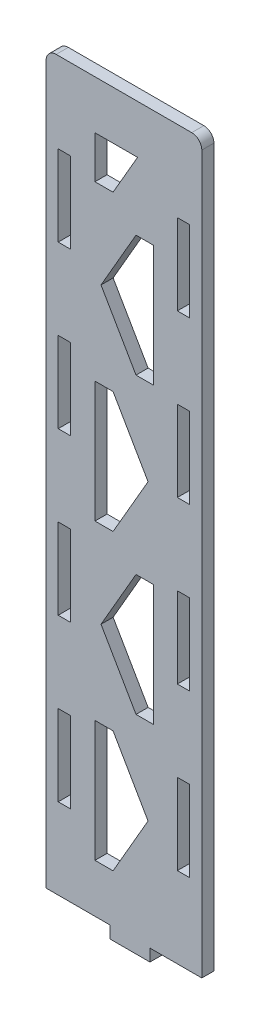
SolidWorks part; units mm, degrees
ref_plane "Front Plane" through (0, 0, 0) normal (0, 0, 1) x (1, 0, 0)
ref_plane "Top Plane" through (0, 0, 0) normal (0, 1, 0) x (1, 0, 0)
ref_plane "Right Plane" through (0, 0, 0) normal (1, 0, 0) x (0, 0, -1)
sketch "Sketch1" plane through (0, 0, 0) normal (0, 0, 1) x (1, 0, 0)
  line L0 (-16.275, -90) -> (-16.275, 90) construction
  line L1 (-19.275, -90) -> (19.275, -90)
  line L2 (-19.275, -90) -> (-19.275, 90)
  line L3 (-19.275, 90) -> (19.275, 90)
  line L4 (19.275, -90) -> (19.275, 90)
  line L5 (-19.275, -90) -> (19.275, 90) construction
  line L6 (-19.275, 90) -> (19.275, -90) construction
  line L7 (16.275, -90) -> (16.275, 90) construction
  line L8 (6.4417, -93) -> (16.275, -93) construction
  line L33 (-3.3917, -93) -> (6.4417, -93)
  line L34 (-3.3917, -93) -> (-3.3917, -90)
  line L35 (-3.3917, -90) -> (6.4417, -90)
  line L36 (6.4417, -93) -> (6.4417, -90)
  line L37 (-3.3917, -93) -> (6.4417, -90) construction
  line L38 (-3.3917, -90) -> (6.4417, -93) construction
  line L43 (-3.3917, -93) -> (-13.225, -93) construction
  line L44 (13.225, 90) -> (13.225, 70) construction
  line L45 (13.225, -10) -> (16.275, -10)
  line L46 (13.225, -10) -> (13.225, -30)
  line L47 (13.225, -30) -> (16.275, -30)
  line L48 (16.275, -10) -> (16.275, -30)
  line L49 (13.225, -10) -> (16.275, -30) construction
  line L50 (13.225, -30) -> (16.275, -10) construction
  line L51 (13.225, 10) -> (16.275, 10)
  line L52 (13.225, 10) -> (13.225, 30)
  line L53 (13.225, 30) -> (16.275, 30)
  line L54 (16.275, 10) -> (16.275, 30)
  line L55 (13.225, 10) -> (16.275, 30) construction
  line L56 (13.225, 30) -> (16.275, 10) construction
  line L57 (13.225, 50) -> (16.275, 50)
  line L58 (13.225, 50) -> (13.225, 70)
  line L59 (13.225, 70) -> (16.275, 70)
  line L60 (16.275, 50) -> (16.275, 70)
  line L61 (13.225, 50) -> (16.275, 70) construction
  line L62 (13.225, 70) -> (16.275, 50) construction
  line L63 (13.225, -50) -> (16.275, -50)
  line L64 (13.225, -50) -> (13.225, -70)
  line L65 (13.225, -70) -> (16.275, -70)
  line L66 (16.275, -50) -> (16.275, -70)
  line L67 (13.225, -50) -> (16.275, -70) construction
  line L68 (13.225, -70) -> (16.275, -50) construction
  line L69 (13.225, 50) -> (13.225, 30) construction
  line L70 (13.225, 10) -> (13.225, -10) construction
  line L71 (13.225, -30) -> (13.225, -50) construction
  line L72 (13.225, -70) -> (13.225, -90) construction
  line L73 (0, -781.5075) -> (0, 49218.4925) construction
  line L74 (-13.225, 70) -> (-16.275, 70)
  line L75 (-16.275, 50) -> (-16.275, 70)
  line L76 (-13.225, 50) -> (-16.275, 50)
  line L77 (-13.225, 50) -> (-13.225, 70)
  line L78 (-13.225, 30) -> (-16.275, 30)
  line L79 (-16.275, 10) -> (-16.275, 30)
  line L80 (-13.225, 10) -> (-16.275, 10)
  line L81 (-13.225, 10) -> (-13.225, 30)
  line L82 (-13.225, -30) -> (-16.275, -30)
  line L83 (-16.275, -10) -> (-16.275, -30)
  line L84 (-13.225, -10) -> (-16.275, -10)
  line L85 (-13.225, -10) -> (-13.225, -30)
  line L86 (-13.225, -70) -> (-16.275, -70)
  line L87 (-16.275, -50) -> (-16.275, -70)
  line L88 (-13.225, -50) -> (-16.275, -50)
  line L89 (-13.225, -50) -> (-13.225, -70)
  point P0 (0, 0)
  point P30 (1.525, -91.5)
  point P35 (14.75, 20)
  point P39 (14.75, -20)
  point P47 (14.75, 60)
  point P52 (14.75, -60)
  dimension "D1" = 26.45
  dimension "D2" = 180
  dimension "D5" = 3
  dimension "D6" = 3.05
  dimension "D3" = 3
  dimension "D4" = 3
extrude "Boss-Extrude1" add sketch "Sketch1" along normal blind 3
sketch "Sketch2" plane through (-113.675, -93, 3) normal (0, 0, -1) x (-1, 0, 0)
  line L1 (-234.6603, 8.6269) -> (-251.9808, 8.6269)
  line L2 (-251.9808, 8.6269) -> (-260.641, -6.3731)
  line L3 (-260.641, -6.3731) -> (-251.9808, -21.3731)
  line L4 (-251.9808, -21.3731) -> (-234.6603, -21.3731)
  line L5 (-234.6603, -21.3731) -> (-226, -6.3731)
  line L6 (-226, -6.3731) -> (-234.6603, 8.6269)
  line L7 (-192.6603, 8.6269) -> (-209.9808, 8.6269)
  line L8 (-209.9808, 8.6269) -> (-218.641, -6.3731)
  line L9 (-218.641, -6.3731) -> (-209.9808, -21.3731)
  line L10 (-209.9808, -21.3731) -> (-192.6603, -21.3731)
  line L11 (-192.6603, -21.3731) -> (-184, -6.3731)
  line L12 (-184, -6.3731) -> (-192.6603, 8.6269)
  line L13 (-150.6603, 8.6269) -> (-167.9808, 8.6269)
  line L14 (-167.9808, 8.6269) -> (-176.641, -6.3731)
  line L15 (-176.641, -6.3731) -> (-167.9808, -21.3731)
  line L16 (-167.9808, -21.3731) -> (-150.6603, -21.3731)
  line L17 (-150.6603, -21.3731) -> (-142, -6.3731)
  line L18 (-142, -6.3731) -> (-150.6603, 8.6269)
  line L19 (-108.6603, 8.6269) -> (-125.9808, 8.6269)
  line L20 (-125.9808, 8.6269) -> (-134.641, -6.3731)
  line L21 (-134.641, -6.3731) -> (-125.9808, -21.3731)
  line L22 (-125.9808, -21.3731) -> (-108.6603, -21.3731)
  line L23 (-108.6603, -21.3731) -> (-100, -6.3731)
  line L24 (-100, -6.3731) -> (-108.6603, 8.6269)
  line L25 (-66.6603, 8.6269) -> (-83.9808, 8.6269)
  line L26 (-83.9808, 8.6269) -> (-92.641, -6.3731)
  line L27 (-92.641, -6.3731) -> (-83.9808, -21.3731)
  line L28 (-83.9808, -21.3731) -> (-66.6603, -21.3731)
  line L29 (-66.6603, -21.3731) -> (-58, -6.3731)
  line L30 (-58, -6.3731) -> (-66.6603, 8.6269)
  line L31 (-24.6603, 8.6269) -> (-41.9808, 8.6269)
  line L32 (-41.9808, 8.6269) -> (-50.641, -6.3731)
  line L33 (-50.641, -6.3731) -> (-41.9808, -21.3731)
  line L34 (-41.9808, -21.3731) -> (-24.6603, -21.3731)
  line L35 (-24.6603, -21.3731) -> (-16, -6.3731)
  line L36 (-16, -6.3731) -> (-24.6603, 8.6269)
  line L37 (17.3397, 8.6269) -> (0.0192, 8.6269)
  line L38 (0.0192, 8.6269) -> (-8.641, -6.3731)
  line L39 (-8.641, -6.3731) -> (0.0192, -21.3731)
  line L40 (0.0192, -21.3731) -> (17.3397, -21.3731)
  line L41 (17.3397, -21.3731) -> (26, -6.3731)
  line L42 (26, -6.3731) -> (17.3397, 8.6269)
  line L43 (59.3397, 8.6269) -> (42.0192, 8.6269)
  line L44 (42.0192, 8.6269) -> (33.359, -6.3731)
  line L45 (33.359, -6.3731) -> (42.0192, -21.3731)
  line L46 (42.0192, -21.3731) -> (59.3397, -21.3731)
  line L47 (59.3397, -21.3731) -> (68, -6.3731)
  line L48 (68, -6.3731) -> (59.3397, 8.6269)
  line L49 (-171.6603, 45) -> (-188.9808, 45)
  line L50 (-188.9808, 45) -> (-197.641, 30)
  line L51 (-197.641, 30) -> (-188.9808, 15)
  line L52 (-188.9808, 15) -> (-171.6603, 15)
  line L53 (-171.6603, 15) -> (-163, 30)
  line L54 (-163, 30) -> (-171.6603, 45)
  line L55 (-129.6603, 45) -> (-146.9808, 45)
  line L56 (-146.9808, 45) -> (-155.641, 30)
  line L57 (-155.641, 30) -> (-146.9808, 15)
  line L58 (-146.9808, 15) -> (-129.6603, 15)
  line L59 (-129.6603, 15) -> (-121, 30)
  line L60 (-121, 30) -> (-129.6603, 45)
  line L61 (-87.6603, 45) -> (-104.9808, 45)
  line L62 (-104.9808, 45) -> (-113.641, 30)
  line L63 (-113.641, 30) -> (-104.9808, 15)
  line L64 (-104.9808, 15) -> (-87.6603, 15)
  line L65 (-87.6603, 15) -> (-79, 30)
  line L66 (-79, 30) -> (-87.6603, 45)
  line L67 (-45.6603, 45) -> (-62.9808, 45)
  line L68 (-62.9808, 45) -> (-71.641, 30)
  line L69 (-71.641, 30) -> (-62.9808, 15)
  line L70 (-62.9808, 15) -> (-45.6603, 15)
  line L71 (-45.6603, 15) -> (-37, 30)
  line L72 (-37, 30) -> (-45.6603, 45)
  line L73 (-3.6603, 45) -> (-20.9808, 45)
  line L74 (-20.9808, 45) -> (-29.641, 30)
  line L75 (-29.641, 30) -> (-20.9808, 15)
  line L76 (-20.9808, 15) -> (-3.6603, 15)
  line L77 (-3.6603, 15) -> (5, 30)
  line L78 (5, 30) -> (-3.6603, 45)
  line L79 (38.3397, 45) -> (21.0192, 45)
  line L80 (21.0192, 45) -> (12.359, 30)
  line L81 (12.359, 30) -> (21.0192, 15)
  line L82 (21.0192, 15) -> (38.3397, 15)
  line L83 (38.3397, 15) -> (47, 30)
  line L84 (47, 30) -> (38.3397, 45)
  line L85 (80.3397, 45) -> (63.0192, 45)
  line L86 (63.0192, 45) -> (54.359, 30)
  line L87 (54.359, 30) -> (63.0192, 15)
  line L88 (63.0192, 15) -> (80.3397, 15)
  line L89 (80.3397, 15) -> (89, 30)
  line L90 (89, 30) -> (80.3397, 45)
  line L91 (-150.6603, 81.3731) -> (-167.9808, 81.3731)
  line L92 (-167.9808, 81.3731) -> (-176.641, 66.3731)
  line L93 (-176.641, 66.3731) -> (-167.9808, 51.3731)
  line L94 (-167.9808, 51.3731) -> (-150.6603, 51.3731)
  line L95 (-150.6603, 51.3731) -> (-142, 66.3731)
  line L96 (-142, 66.3731) -> (-150.6603, 81.3731)
  line L97 (-108.6603, 81.3731) -> (-125.9808, 81.3731)
  line L98 (-125.9808, 81.3731) -> (-134.641, 66.3731)
  line L99 (-134.641, 66.3731) -> (-125.9808, 51.3731)
  line L100 (-125.9808, 51.3731) -> (-108.6603, 51.3731)
  line L101 (-108.6603, 51.3731) -> (-100, 66.3731)
  line L102 (-100, 66.3731) -> (-108.6603, 81.3731)
  line L103 (-66.6603, 81.3731) -> (-83.9808, 81.3731)
  line L104 (-83.9808, 81.3731) -> (-92.641, 66.3731)
  line L105 (-92.641, 66.3731) -> (-83.9808, 51.3731)
  line L106 (-83.9808, 51.3731) -> (-66.6603, 51.3731)
  line L107 (-66.6603, 51.3731) -> (-58, 66.3731)
  line L108 (-58, 66.3731) -> (-66.6603, 81.3731)
  line L109 (-24.6603, 81.3731) -> (-41.9808, 81.3731)
  line L110 (-41.9808, 81.3731) -> (-50.641, 66.3731)
  line L111 (-50.641, 66.3731) -> (-41.9808, 51.3731)
  line L112 (-41.9808, 51.3731) -> (-24.6603, 51.3731)
  line L113 (-24.6603, 51.3731) -> (-16, 66.3731)
  line L114 (-16, 66.3731) -> (-24.6603, 81.3731)
  line L115 (17.3397, 81.3731) -> (0.0192, 81.3731)
  line L116 (0.0192, 81.3731) -> (-8.641, 66.3731)
  line L117 (-8.641, 66.3731) -> (0.0192, 51.3731)
  line L118 (0.0192, 51.3731) -> (17.3397, 51.3731)
  line L119 (17.3397, 51.3731) -> (26, 66.3731)
  line L120 (26, 66.3731) -> (17.3397, 81.3731)
  line L121 (59.3397, 81.3731) -> (42.0192, 81.3731)
  line L122 (42.0192, 81.3731) -> (33.359, 66.3731)
  line L123 (33.359, 66.3731) -> (42.0192, 51.3731)
  line L124 (42.0192, 51.3731) -> (59.3397, 51.3731)
  line L125 (59.3397, 51.3731) -> (68, 66.3731)
  line L126 (68, 66.3731) -> (59.3397, 81.3731)
  line L127 (101.3397, 81.3731) -> (84.0192, 81.3731)
  line L128 (84.0192, 81.3731) -> (75.359, 66.3731)
  line L129 (75.359, 66.3731) -> (84.0192, 51.3731)
  line L130 (84.0192, 51.3731) -> (101.3397, 51.3731)
  line L131 (101.3397, 51.3731) -> (110, 66.3731)
  line L132 (110, 66.3731) -> (101.3397, 81.3731)
  line L133 (-129.6603, 117.7461) -> (-146.9808, 117.7461)
  line L134 (-146.9808, 117.7461) -> (-155.641, 102.7461)
  line L135 (-155.641, 102.7461) -> (-146.9808, 87.7461)
  line L136 (-146.9808, 87.7461) -> (-129.6603, 87.7461)
  line L137 (-129.6603, 87.7461) -> (-121, 102.7461)
  line L138 (-121, 102.7461) -> (-129.6603, 117.7461)
  line L139 (-87.6603, 117.7461) -> (-104.9808, 117.7461)
  line L140 (-104.9808, 117.7461) -> (-113.641, 102.7461)
  line L141 (-113.641, 102.7461) -> (-104.9808, 87.7461)
  line L142 (-104.9808, 87.7461) -> (-87.6603, 87.7461)
  line L143 (-87.6603, 87.7461) -> (-79, 102.7461)
  line L144 (-79, 102.7461) -> (-87.6603, 117.7461)
  line L145 (-45.6603, 117.7461) -> (-62.9808, 117.7461)
  line L146 (-62.9808, 117.7461) -> (-71.641, 102.7461)
  line L147 (-71.641, 102.7461) -> (-62.9808, 87.7461)
  line L148 (-62.9808, 87.7461) -> (-45.6603, 87.7461)
  line L149 (-45.6603, 87.7461) -> (-37, 102.7461)
  line L150 (-37, 102.7461) -> (-45.6603, 117.7461)
  line L151 (-3.6603, 117.7461) -> (-20.9808, 117.7461)
  line L152 (-20.9808, 117.7461) -> (-29.641, 102.7461)
  line L153 (-29.641, 102.7461) -> (-20.9808, 87.7461)
  line L154 (-20.9808, 87.7461) -> (-3.6603, 87.7461)
  line L155 (-3.6603, 87.7461) -> (5, 102.7461)
  line L156 (5, 102.7461) -> (-3.6603, 117.7461)
  line L157 (38.3397, 117.7461) -> (21.0192, 117.7461)
  line L158 (21.0192, 117.7461) -> (12.359, 102.7461)
  line L159 (12.359, 102.7461) -> (21.0192, 87.7461)
  line L160 (21.0192, 87.7461) -> (38.3397, 87.7461)
  line L161 (38.3397, 87.7461) -> (47, 102.7461)
  line L162 (47, 102.7461) -> (38.3397, 117.7461)
  line L163 (80.3397, 117.7461) -> (63.0192, 117.7461)
  line L164 (63.0192, 117.7461) -> (54.359, 102.7461)
  line L165 (54.359, 102.7461) -> (63.0192, 87.7461)
  line L166 (63.0192, 87.7461) -> (80.3397, 87.7461)
  line L167 (80.3397, 87.7461) -> (89, 102.7461)
  line L168 (89, 102.7461) -> (80.3397, 117.7461)
  line L169 (122.3397, 117.7461) -> (105.0192, 117.7461)
  line L170 (105.0192, 117.7461) -> (96.359, 102.7461)
  line L171 (96.359, 102.7461) -> (105.0192, 87.7461)
  line L172 (105.0192, 87.7461) -> (122.3397, 87.7461)
  line L173 (122.3397, 87.7461) -> (131, 102.7461)
  line L174 (131, 102.7461) -> (122.3397, 117.7461)
  line L175 (-108.6603, 154.1192) -> (-125.9808, 154.1192)
  line L176 (-125.9808, 154.1192) -> (-134.641, 139.1192)
  line L177 (-134.641, 139.1192) -> (-125.9808, 124.1192)
  line L178 (-125.9808, 124.1192) -> (-108.6603, 124.1192)
  line L179 (-108.6603, 124.1192) -> (-100, 139.1192)
  line L180 (-100, 139.1192) -> (-108.6603, 154.1192)
  line L181 (-66.6603, 154.1192) -> (-83.9808, 154.1192)
  line L182 (-83.9808, 154.1192) -> (-92.641, 139.1192)
  line L183 (-92.641, 139.1192) -> (-83.9808, 124.1192)
  line L184 (-83.9808, 124.1192) -> (-66.6603, 124.1192)
  line L185 (-66.6603, 124.1192) -> (-58, 139.1192)
  line L186 (-58, 139.1192) -> (-66.6603, 154.1192)
  line L187 (-24.6603, 154.1192) -> (-41.9808, 154.1192)
  line L188 (-41.9808, 154.1192) -> (-50.641, 139.1192)
  line L189 (-50.641, 139.1192) -> (-41.9808, 124.1192)
  line L190 (-41.9808, 124.1192) -> (-24.6603, 124.1192)
  line L191 (-24.6603, 124.1192) -> (-16, 139.1192)
  line L192 (-16, 139.1192) -> (-24.6603, 154.1192)
  line L193 (17.3397, 154.1192) -> (0.0192, 154.1192)
  line L194 (0.0192, 154.1192) -> (-8.641, 139.1192)
  line L195 (-8.641, 139.1192) -> (0.0192, 124.1192)
  line L196 (0.0192, 124.1192) -> (17.3397, 124.1192)
  line L197 (17.3397, 124.1192) -> (26, 139.1192)
  line L198 (26, 139.1192) -> (17.3397, 154.1192)
  line L199 (59.3397, 154.1192) -> (42.0192, 154.1192)
  line L200 (42.0192, 154.1192) -> (33.359, 139.1192)
  line L201 (33.359, 139.1192) -> (42.0192, 124.1192)
  line L202 (42.0192, 124.1192) -> (59.3397, 124.1192)
  line L203 (59.3397, 124.1192) -> (68, 139.1192)
  line L204 (68, 139.1192) -> (59.3397, 154.1192)
  line L205 (101.3397, 154.1192) -> (84.0192, 154.1192)
  line L206 (84.0192, 154.1192) -> (75.359, 139.1192)
  line L207 (75.359, 139.1192) -> (84.0192, 124.1192)
  line L208 (84.0192, 124.1192) -> (101.3397, 124.1192)
  line L209 (101.3397, 124.1192) -> (110, 139.1192)
  line L210 (110, 139.1192) -> (101.3397, 154.1192)
  line L211 (143.3397, 154.1192) -> (126.0192, 154.1192)
  line L212 (126.0192, 154.1192) -> (117.359, 139.1192)
  line L213 (117.359, 139.1192) -> (126.0192, 124.1192)
  line L214 (126.0192, 124.1192) -> (143.3397, 124.1192)
  line L215 (143.3397, 124.1192) -> (152, 139.1192)
  line L216 (152, 139.1192) -> (143.3397, 154.1192)
  line L217 (-87.6603, 190.4923) -> (-104.9808, 190.4923)
  line L218 (-104.9808, 190.4923) -> (-113.641, 175.4923)
  line L219 (-113.641, 175.4923) -> (-104.9808, 160.4923)
  line L220 (-104.9808, 160.4923) -> (-87.6603, 160.4923)
  line L221 (-87.6603, 160.4923) -> (-79, 175.4923)
  line L222 (-79, 175.4923) -> (-87.6603, 190.4923)
  line L223 (-45.6603, 190.4923) -> (-62.9808, 190.4923)
  line L224 (-62.9808, 190.4923) -> (-71.641, 175.4923)
  line L225 (-71.641, 175.4923) -> (-62.9808, 160.4923)
  line L226 (-62.9808, 160.4923) -> (-45.6603, 160.4923)
  line L227 (-45.6603, 160.4923) -> (-37, 175.4923)
  line L228 (-37, 175.4923) -> (-45.6603, 190.4923)
  line L229 (-3.6603, 190.4923) -> (-20.9808, 190.4923)
  line L230 (-20.9808, 190.4923) -> (-29.641, 175.4923)
  line L231 (-29.641, 175.4923) -> (-20.9808, 160.4923)
  line L232 (-20.9808, 160.4923) -> (-3.6603, 160.4923)
  line L233 (-3.6603, 160.4923) -> (5, 175.4923)
  line L234 (5, 175.4923) -> (-3.6603, 190.4923)
  line L235 (38.3397, 190.4923) -> (21.0192, 190.4923)
  line L236 (21.0192, 190.4923) -> (12.359, 175.4923)
  line L237 (12.359, 175.4923) -> (21.0192, 160.4923)
  line L238 (21.0192, 160.4923) -> (38.3397, 160.4923)
  line L239 (38.3397, 160.4923) -> (47, 175.4923)
  line L240 (47, 175.4923) -> (38.3397, 190.4923)
  line L241 (80.3397, 190.4923) -> (63.0192, 190.4923)
  line L242 (63.0192, 190.4923) -> (54.359, 175.4923)
  line L243 (54.359, 175.4923) -> (63.0192, 160.4923)
  line L244 (63.0192, 160.4923) -> (80.3397, 160.4923)
  line L245 (80.3397, 160.4923) -> (89, 175.4923)
  line L246 (89, 175.4923) -> (80.3397, 190.4923)
  line L247 (122.3397, 190.4923) -> (105.0192, 190.4923)
  line L248 (105.0192, 190.4923) -> (96.359, 175.4923)
  line L249 (96.359, 175.4923) -> (105.0192, 160.4923)
  line L250 (105.0192, 160.4923) -> (122.3397, 160.4923)
  line L251 (122.3397, 160.4923) -> (131, 175.4923)
  line L252 (131, 175.4923) -> (122.3397, 190.4923)
  line L253 (164.3397, 190.4923) -> (147.0192, 190.4923)
  line L254 (147.0192, 190.4923) -> (138.359, 175.4923)
  line L255 (138.359, 175.4923) -> (147.0192, 160.4923)
  line L256 (147.0192, 160.4923) -> (164.3397, 160.4923)
  line L257 (164.3397, 160.4923) -> (173, 175.4923)
  line L258 (173, 175.4923) -> (164.3397, 190.4923)
  line L343 (-213.6603, 45) -> (-230.9808, 45)
  line L344 (-230.9808, 45) -> (-239.641, 30)
  line L345 (-239.641, 30) -> (-230.9808, 15)
  line L346 (-230.9808, 15) -> (-213.6603, 15)
  line L347 (-213.6603, 15) -> (-205, 30)
  line L348 (-205, 30) -> (-213.6603, 45)
  line L349 (-192.6603, 81.3731) -> (-209.9808, 81.3731)
  line L350 (-209.9808, 81.3731) -> (-218.641, 66.3731)
  line L351 (-218.641, 66.3731) -> (-209.9808, 51.3731)
  line L352 (-209.9808, 51.3731) -> (-192.6603, 51.3731)
  line L353 (-192.6603, 51.3731) -> (-184, 66.3731)
  line L354 (-184, 66.3731) -> (-192.6603, 81.3731)
  line L355 (-171.6603, 117.7461) -> (-188.9808, 117.7461)
  line L356 (-188.9808, 117.7461) -> (-197.641, 102.7461)
  line L357 (-197.641, 102.7461) -> (-188.9808, 87.7461)
  line L358 (-188.9808, 87.7461) -> (-171.6603, 87.7461)
  line L359 (-171.6603, 87.7461) -> (-163, 102.7461)
  line L360 (-163, 102.7461) -> (-171.6603, 117.7461)
  line L361 (-150.6603, 154.1192) -> (-167.9808, 154.1192)
  line L362 (-167.9808, 154.1192) -> (-176.641, 139.1192)
  line L363 (-176.641, 139.1192) -> (-167.9808, 124.1192)
  line L364 (-167.9808, 124.1192) -> (-150.6603, 124.1192)
  line L365 (-150.6603, 124.1192) -> (-142, 139.1192)
  line L366 (-142, 139.1192) -> (-150.6603, 154.1192)
  line L367 (-129.6603, 190.4923) -> (-146.9808, 190.4923)
  line L368 (-146.9808, 190.4923) -> (-155.641, 175.4923)
  line L369 (-155.641, 175.4923) -> (-146.9808, 160.4923)
  line L370 (-146.9808, 160.4923) -> (-129.6603, 160.4923)
  line L371 (-129.6603, 160.4923) -> (-121, 175.4923)
  line L372 (-121, 175.4923) -> (-129.6603, 190.4923)
  line L387 (-226, -6.3731) -> (-218.641, -6.3731) construction
  line L388 (-209.9808, 8.6269) -> (-213.6603, 15) construction
  line L389 (-234.6603, 8.6269) -> (-230.9808, 15) construction
  line L390 (101.3397, 8.6269) -> (84.0192, 8.6269)
  line L391 (84.0192, 8.6269) -> (75.359, -6.3731)
  line L392 (75.359, -6.3731) -> (84.0192, -21.3731)
  line L393 (84.0192, -21.3731) -> (101.3397, -21.3731)
  line L394 (101.3397, -21.3731) -> (110, -6.3731)
  line L395 (110, -6.3731) -> (101.3397, 8.6269)
  line L396 (143.3397, 8.6269) -> (126.0192, 8.6269)
  line L397 (126.0192, 8.6269) -> (117.359, -6.3731)
  line L398 (117.359, -6.3731) -> (126.0192, -21.3731)
  line L399 (126.0192, -21.3731) -> (143.3397, -21.3731)
  line L400 (143.3397, -21.3731) -> (152, -6.3731)
  line L401 (152, -6.3731) -> (143.3397, 8.6269)
  line L402 (185.3397, 8.6269) -> (168.0192, 8.6269)
  line L403 (168.0192, 8.6269) -> (159.359, -6.3731)
  line L404 (159.359, -6.3731) -> (168.0192, -21.3731)
  line L405 (168.0192, -21.3731) -> (185.3397, -21.3731)
  line L406 (185.3397, -21.3731) -> (194, -6.3731)
  line L407 (194, -6.3731) -> (185.3397, 8.6269)
  line L414 (122.3397, 45) -> (105.0192, 45)
  line L415 (105.0192, 45) -> (96.359, 30)
  line L416 (96.359, 30) -> (105.0192, 15)
  line L417 (105.0192, 15) -> (122.3397, 15)
  line L418 (122.3397, 15) -> (131, 30)
  line L419 (131, 30) -> (122.3397, 45)
  line L420 (164.3397, 45) -> (147.0192, 45)
  line L421 (147.0192, 45) -> (138.359, 30)
  line L422 (138.359, 30) -> (147.0192, 15)
  line L423 (147.0192, 15) -> (164.3397, 15)
  line L424 (164.3397, 15) -> (173, 30)
  line L425 (173, 30) -> (164.3397, 45)
  line L426 (206.3397, 45) -> (189.0192, 45)
  line L427 (189.0192, 45) -> (180.359, 30)
  line L428 (180.359, 30) -> (189.0192, 15)
  line L429 (189.0192, 15) -> (206.3397, 15)
  line L430 (206.3397, 15) -> (215, 30)
  line L431 (215, 30) -> (206.3397, 45)
  line L438 (143.3397, 81.3731) -> (126.0192, 81.3731)
  line L439 (126.0192, 81.3731) -> (117.359, 66.3731)
  line L440 (117.359, 66.3731) -> (126.0192, 51.3731)
  line L441 (126.0192, 51.3731) -> (143.3397, 51.3731)
  line L442 (143.3397, 51.3731) -> (152, 66.3731)
  line L443 (152, 66.3731) -> (143.3397, 81.3731)
  line L444 (185.3397, 81.3731) -> (168.0192, 81.3731)
  line L445 (168.0192, 81.3731) -> (159.359, 66.3731)
  line L446 (159.359, 66.3731) -> (168.0192, 51.3731)
  line L447 (168.0192, 51.3731) -> (185.3397, 51.3731)
  line L448 (185.3397, 51.3731) -> (194, 66.3731)
  line L449 (194, 66.3731) -> (185.3397, 81.3731)
  line L450 (227.3397, 81.3731) -> (210.0192, 81.3731)
  line L451 (210.0192, 81.3731) -> (201.359, 66.3731)
  line L452 (201.359, 66.3731) -> (210.0192, 51.3731)
  line L453 (210.0192, 51.3731) -> (227.3397, 51.3731)
  line L454 (227.3397, 51.3731) -> (236, 66.3731)
  line L455 (236, 66.3731) -> (227.3397, 81.3731)
  line L462 (164.3397, 117.7461) -> (147.0192, 117.7461)
  line L463 (147.0192, 117.7461) -> (138.359, 102.7461)
  line L464 (138.359, 102.7461) -> (147.0192, 87.7461)
  line L465 (147.0192, 87.7461) -> (164.3397, 87.7461)
  line L466 (164.3397, 87.7461) -> (173, 102.7461)
  line L467 (173, 102.7461) -> (164.3397, 117.7461)
  line L468 (206.3397, 117.7461) -> (189.0192, 117.7461)
  line L469 (189.0192, 117.7461) -> (180.359, 102.7461)
  line L470 (180.359, 102.7461) -> (189.0192, 87.7461)
  line L471 (189.0192, 87.7461) -> (206.3397, 87.7461)
  line L472 (206.3397, 87.7461) -> (215, 102.7461)
  line L473 (215, 102.7461) -> (206.3397, 117.7461)
  line L474 (248.3397, 117.7461) -> (231.0192, 117.7461)
  line L475 (231.0192, 117.7461) -> (222.359, 102.7461)
  line L476 (222.359, 102.7461) -> (231.0192, 87.7461)
  line L477 (231.0192, 87.7461) -> (248.3397, 87.7461)
  line L478 (248.3397, 87.7461) -> (257, 102.7461)
  line L479 (257, 102.7461) -> (248.3397, 117.7461)
  line L486 (185.3397, 154.1192) -> (168.0192, 154.1192)
  line L487 (168.0192, 154.1192) -> (159.359, 139.1192)
  line L488 (159.359, 139.1192) -> (168.0192, 124.1192)
  line L489 (168.0192, 124.1192) -> (185.3397, 124.1192)
  line L490 (185.3397, 124.1192) -> (194, 139.1192)
  line L491 (194, 139.1192) -> (185.3397, 154.1192)
  line L492 (227.3397, 154.1192) -> (210.0192, 154.1192)
  line L493 (210.0192, 154.1192) -> (201.359, 139.1192)
  line L494 (201.359, 139.1192) -> (210.0192, 124.1192)
  line L495 (210.0192, 124.1192) -> (227.3397, 124.1192)
  line L496 (227.3397, 124.1192) -> (236, 139.1192)
  line L497 (236, 139.1192) -> (227.3397, 154.1192)
  line L498 (269.3397, 154.1192) -> (252.0192, 154.1192)
  line L499 (252.0192, 154.1192) -> (243.359, 139.1192)
  line L500 (243.359, 139.1192) -> (252.0192, 124.1192)
  line L501 (252.0192, 124.1192) -> (269.3397, 124.1192)
  line L502 (269.3397, 124.1192) -> (278, 139.1192)
  line L503 (278, 139.1192) -> (269.3397, 154.1192)
  line L510 (206.3397, 190.4923) -> (189.0192, 190.4923)
  line L511 (189.0192, 190.4923) -> (180.359, 175.4923)
  line L512 (180.359, 175.4923) -> (189.0192, 160.4923)
  line L513 (189.0192, 160.4923) -> (206.3397, 160.4923)
  line L514 (206.3397, 160.4923) -> (215, 175.4923)
  line L515 (215, 175.4923) -> (206.3397, 190.4923)
  line L516 (248.3397, 190.4923) -> (231.0192, 190.4923)
  line L517 (231.0192, 190.4923) -> (222.359, 175.4923)
  line L518 (222.359, 175.4923) -> (231.0192, 160.4923)
  line L519 (231.0192, 160.4923) -> (248.3397, 160.4923)
  line L520 (248.3397, 160.4923) -> (257, 175.4923)
  line L521 (257, 175.4923) -> (248.3397, 190.4923)
  line L522 (290.3397, 190.4923) -> (273.0192, 190.4923)
  line L523 (273.0192, 190.4923) -> (264.359, 175.4923)
  line L524 (264.359, 175.4923) -> (273.0192, 160.4923)
  line L525 (273.0192, 160.4923) -> (290.3397, 160.4923)
  line L526 (290.3397, 160.4923) -> (299, 175.4923)
  line L527 (299, 175.4923) -> (290.3397, 190.4923)
  line L534 (-121, 171) -> (-121, 15)
  line L535 (-121, 15) -> (121, 15)
  line L538 (121, 171) -> (-121, 171)
  line L544 (121, 171) -> (121, 15)
  line L551 (91.5, 131) -> (-91.5, 131)
  line L552 (-91.5, 131) -> (-91.5, 15)
  line L553 (-91.5, 15) -> (91.5, 15)
  line L554 (91.5, 15) -> (91.5, 131)
  line L560 (106.5, 171) -> (106.5, 15)
  line L561 (-106.5, 171) -> (-106.5, 15)
  circle A0 centre (-243.3205, -6.3731) radius 15 construction
sketch "Sketch3" plane through (0, 0, 3) normal (0, 0, 1) x (1, 0, 0)
  line L0 (12.3058, 31.1192) -> (-5.0147, 31.1192) construction
  line L9 (2.9853, 31.1192) -> (-5.675, 46.1192)
  line L10 (-5.675, 46.1192) -> (2.9853, 61.1192)
  line L11 (-5.0147, 61.1192) -> (12.3058, 61.1192) construction
  line L12 (2.9853, -41.6269) -> (-5.675, -26.6269)
  line L13 (12.3058, -41.6269) -> (-5.0147, -41.6269) construction
  line L14 (-5.675, -26.6269) -> (2.9853, -11.6269)
  line L15 (-5.0147, -11.6269) -> (12.3058, -11.6269) construction
  line L16 (-5.0147, 31.1192) -> (-13.675, 46.1192) construction
  line L17 (-5.0147, -41.6269) -> (-13.675, -26.6269) construction
  line L18 (7.325, 78) -> (7.325, -78) construction
  line L19 (2.9853, 61.1192) -> (7.325, 61.1192)
  line L20 (7.325, 61.1192) -> (7.325, 31.1192)
  line L21 (7.325, 31.1192) -> (2.9853, 31.1192)
  line L22 (2.9853, -11.6269) -> (7.325, -11.6269)
  line L23 (7.325, -11.6269) -> (7.325, -41.6269)
  line L24 (7.325, -41.6269) -> (2.9853, -41.6269)
  line L25 (-7.175, 67.4923) -> (-2.6942, 67.4923)
  line L26 (-7.175, 78) -> (-7.175, -78) construction
  line L27 (-2.6942, 67.4923) -> (3.3724, 78)
  line L28 (-234.675, 78) -> (7.325, 78) construction
  line L29 (3.3724, 78) -> (-7.175, 78)
  line L30 (-7.175, 78) -> (-7.175, 67.4923)
  line L31 (-7.175, 24.7461) -> (-2.6942, 24.7461)
  line L32 (-2.6942, 24.7461) -> (5.966, 9.7461)
  line L33 (5.966, 9.7461) -> (-2.6942, -5.2539)
  line L34 (-2.6942, -5.2539) -> (-7.175, -5.2539)
  line L35 (-8.6942, -5.2539) -> (-26.0147, -5.2539) construction
  line L36 (-26.0147, 24.7461) -> (-8.6942, 24.7461) construction
  line L37 (-0.034, 9.7461) -> (-8.6942, -5.2539) construction
  line L38 (-8.6942, 24.7461) -> (-0.034, 9.7461) construction
  line L39 (-7.175, -5.2539) -> (-7.175, 24.7461)
  line L40 (-7.175, -78) -> (-7.175, -48)
  line L41 (-7.175, -48) -> (-2.6942, -48)
  line L42 (-2.6942, -48) -> (5.966, -63)
  line L43 (5.966, -63) -> (-2.6942, -78)
  line L44 (-2.6942, -78) -> (-7.175, -78)
  line L45 (-8.6942, -78) -> (-26.0147, -78) construction
  line L46 (-0.034, -63) -> (-8.6942, -78) construction
  line L47 (-8.6942, -48) -> (-0.034, -63) construction
  line L48 (-26.0147, -48) -> (-8.6942, -48) construction
  line L49 (-8.6942, 67.4923) -> (-26.0147, 67.4923) construction
  dimension "D1" = 8
  dimension "D2" = 6
extrude "Cut-Extrude4" cut sketch "Sketch3" against normal through all both and the other way through all
fillet "Fillet1" radius 2.5 2 edges at (-19.275, 90, 1.5) (19.275, 90, 1.5)
